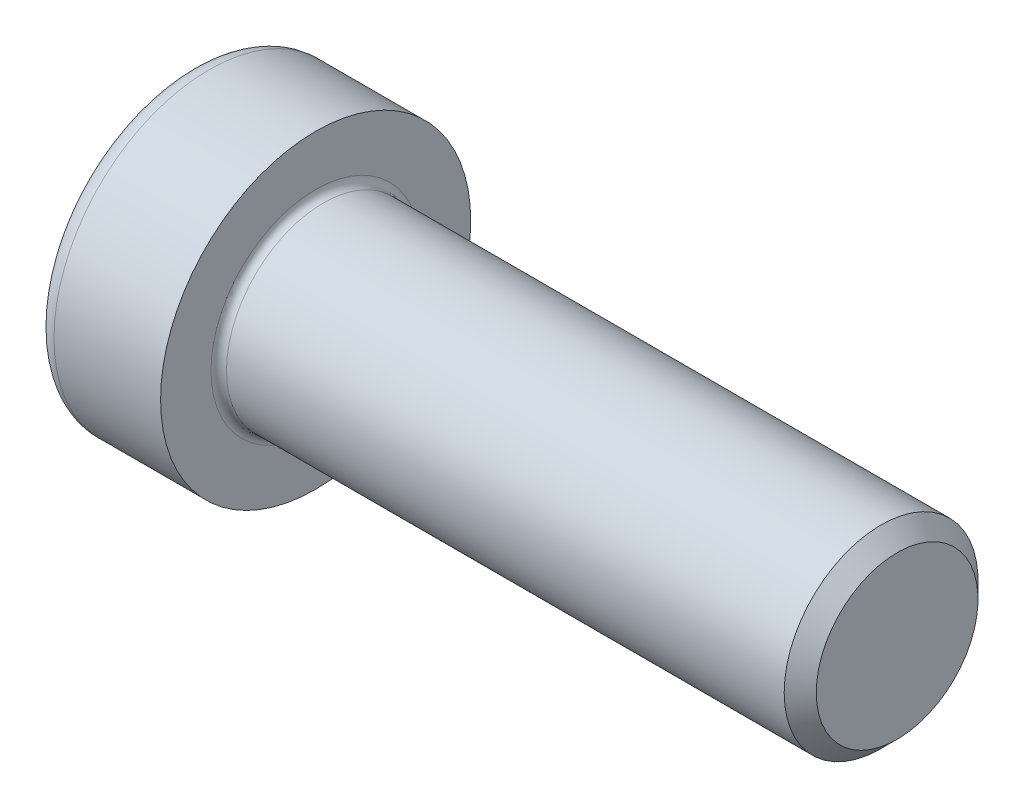
SolidWorks part; units mm, degrees
ref_plane "Plane1" through (0, 0, 0) normal (0, 0, 1) x (1, 0, 0)
ref_plane "Plane2" through (0, 0, 0) normal (0, 1, 0) x (1, 0, 0)
ref_plane "Plane3" through (0, 0, 0) normal (1, 0, 0) x (0, 0, -1)
sketch "BodySke" plane through (0, 0, 0) normal (0, 0, 1) x (1, 0, 0)
  line L0 (0, 0) -> (0, 8)
  line L1 (0, 8) -> (6.5, 8)
  line L2 (6.5, 8) -> (6.5, 5)
  line L3 (6.5, 5) -> (35.672, 5)
  line L4 (36.5, 4.172) -> (36.5, 0)
  line L5 (36.5, 0) -> (0, 0)
  line L6 (-31.75, 0) -> (127, 0) construction
  line L8 (36.5, 4.172) -> (35.672, 5)
  line L10 (36.5, -4.172) -> (35.672, -5) construction
  line L11 (8, 4.525) -> (8, -1.825) construction
  line L12 (6.5, 4.525) -> (6.5, -1.825) construction
  line L13 (-23.5, 4.525) -> (-23.5, -1.825) construction
  dimension "Diameter" = 10
  dimension "Head_ht" = 6.5
  dimension "Length" = 30
  dimension "Body_ch_ang" = 45
  dimension "Head_dia" = 16
  dimension "Minor_dia" = 8.344
  dimension "Advance" = 1.5
  dimension "Thread_nom" = 30
  dimension "Thread_length" = 60
revolve "Base-Revolve" add sketch "BodySke"
cosmetic thread "ThreadCosmetic" [suppressed]
fillet "Fillet1" radius 0.4 1 edges at (6.5, 0, 5)
fillet "Fillet2" radius 1 1 edges at (0, 0, 8)
sketch "HexSke" plane through (0, 0, 0) normal (-1, 0, 0) x (0, 0.5, 0.866)
  line L0 (2.3599, 4.0875) -> (-2.3599, 4.0875)
  line L1 (-2.3599, 4.0875) -> (-4.7198, 0)
  line L2 (2.3599, 4.0875) -> (4.7198, 0)
  line L3 (2.3599, -4.0875) -> (4.7198, 0)
  line L4 (2.3599, -4.0875) -> (-2.3599, -4.0875)
  line L5 (-2.3599, -4.0875) -> (-4.7198, 0)
  dimension "D1" = 4.0875
  dimension "D2" = 4.0875
  dimension "Hex_size" = 8.175
extrude "Hex" cut sketch "HexSke" against normal blind 3.65
sketch "PilotSke" plane through (0, 0, 0) normal (0, 0, 1) x (1, 0, 0)
  line L0 (0, 4.0875) -> (3.65, 4.0875)
  line L1 (3.65, 4.0875) -> (4.5449, 2.5375)
  line L2 (-31.75, 0) -> (127, 0) construction
  line L3 (9.325, 0) -> (0, 0)
  line L4 (0, 0) -> (0, 4.0875)
  line L5 (4.5449, 2.5375) -> (7.86, 2.5375)
  line L6 (0, 0) -> (47.625, 0) construction
  line L7 (7.86, 2.5375) -> (9.325, 0)
  dimension "D1" = 4.0875
  dimension "D2" = 60
  dimension "Depth" = 3.65
  dimension "Pilot_dia" = 5.075
  dimension "Pilot_Depth" = 7.86
revolve "Hex-PreBroach" cut sketch "PilotSke" angle 360 about L6
sketch "ThdSchSke" plane through (0, 0, 0) normal (0, 0, 1) x (1, 0, 0)
  line L0 (11, -4.172) -> (10.4202, -5)
  line L1 (11, -4.172) -> (11.5798, -5)
  line L2 (11.5798, -5) -> (11.5798, -6.25)
  line L3 (-3.175, 0) -> (5.1513, 0) construction
  line L4 (0, 7) -> (0, -7) construction
  line L5 (11.5798, -6.25) -> (10.4202, -6.25)
  line L6 (10.4202, -6.25) -> (10.4202, -5)
  dimension "Thread_minor" = 8.344
  dimension "Diameter" = 10
  dimension "Start" = 11
  dimension "SideAngle" = 55
  dimension "VeeAngle" = 70
  dimension "Overcut" = 12.5
revolve "ThreadSchematic" [suppressed] cut sketch "ThdSchSke" angle 360 about L3
pattern_linear "ThdSchPat" [suppressed]
equation "\"D2@HexSke\" = \"Hex_size@HexSke\" / 2"
equation "\"D1@HexSke\" = \"Hex_size@HexSke\" / 2"
equation "\"D1@PilotSke\" = \"Hex_size@HexSke\" / 2"
equation "\"Thread_minor@ThreadCosmetic\"  =  \"Minor_dia@BodySke\""
equation "\"Depth@PilotSke\" =  \"Key_eng@Hex\""
equation "\"Thread_length@ThreadCosmetic\" = ((sgn( (\"Length@BodySke\" - \"Advance@BodySke\" * 3.0) - \"Thread_nom@BodySke\" )-1)*( (\"Length@BodySke\" - \"Advance@BodySke\" * 3.0) - \"Thread_nom@BodySke\" ))/-2+ \"Thread_nom@BodySke\""
equation "\"Thread_minor@ThdSchSke\" = \"Minor_dia@BodySke\""
equation "\"Diameter@ThdSchSke\" = \"Diameter@BodySke\""
equation "\"Overcut@ThdSchSke\" = \"Diameter@BodySke\" * 1.25"
equation "\"Start@ThdSchSke\" = \"Head_ht@BodySke\" + \"Length@BodySke\" - \"Thread_length@ThreadCosmetic\"  '---Non-countersunk---"
equation "\"Num_threads@ThdSchPat\" = int( \"Thread_length@ThreadCosmetic\" / \"Advance@BodySke\" + 0.999 )  + 1"
equation "\"Advance@ThdSchPat\" = \"Thread_length@ThreadCosmetic\" /  (\"Num_threads@ThdSchPat\" - 1) 'relax it"
equation "\"Num_threads@ThdSchPat\" = \"Num_threads@ThdSchPat\" - sgn( \"Num_threads@ThdSchPat\" - 1) '---chamfered tips only---"
